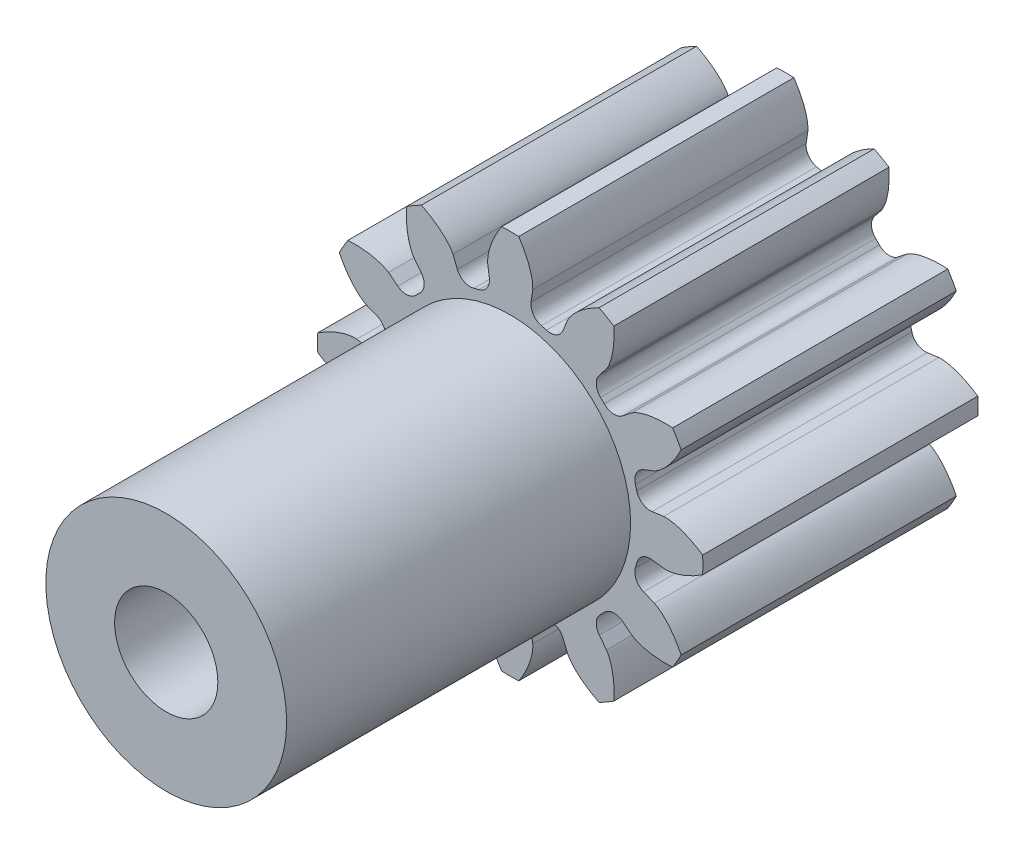
SolidWorks part; units mm, degrees
material "Brass"
ref_plane "Front Plane" through (0, 0, 0) normal (0, 0, 1) x (1, 0, 0)
ref_plane "Top Plane" through (0, 0, 0) normal (0, 1, 0) x (1, 0, 0)
ref_plane "Right Plane" through (0, 0, 0) normal (1, 0, 0) x (0, 0, -1)
ref_plane "Plane1" through (0, 0, 0) normal (0, 0, -1) x (-1, 0, 0)
sketch "Sketch1" plane through (0, 0, 0) normal (0, 0, -1) x (-1, 0, 0)
  line L0 (-2.3524, -2.9706) -> (-2.7989, -3.5371)
  line L1 (-1.6638, -4.1924) -> (-1.3964, -3.5225)
  line L2 (-0.5519, -3.7488) -> (-0.6553, -4.4627)
  line L3 (0.6553, -4.4627) -> (0.5519, -3.7488)
  line L4 (1.3964, -3.5225) -> (1.6638, -4.1924)
  line L5 (2.7989, -3.5371) -> (2.3524, -2.9706)
  line L6 (2.9706, -2.3524) -> (3.5371, -2.7989)
  line L7 (4.1924, -1.6638) -> (3.5225, -1.3964)
  line L8 (3.7488, -0.5519) -> (4.4627, -0.6553)
  line L9 (4.4627, 0.6553) -> (3.7488, 0.5519)
  line L10 (3.5225, 1.3964) -> (4.1924, 1.6638)
  line L11 (3.5371, 2.7989) -> (2.9706, 2.3524)
  line L12 (2.3524, 2.9706) -> (2.7989, 3.5371)
  line L13 (1.6638, 4.1924) -> (1.3964, 3.5225)
  line L14 (0.5519, 3.7488) -> (0.6553, 4.4627)
  line L15 (-0.6553, 4.4627) -> (-0.5519, 3.7488)
  line L16 (-1.3964, 3.5225) -> (-1.6638, 4.1924)
  line L17 (-2.7989, 3.5371) -> (-2.3524, 2.9706)
  line L18 (-2.9706, 2.3524) -> (-3.5371, 2.7989)
  line L19 (-4.1924, 1.6638) -> (-3.5225, 1.3964)
  line L20 (-3.7488, 0.5519) -> (-4.4627, 0.6553)
  line L21 (-4.4627, -0.6553) -> (-3.7488, -0.5519)
  line L22 (-3.5225, -1.3964) -> (-4.1924, -1.6638)
  line L23 (-3.5371, -2.7989) -> (-2.9706, -2.3524)
  arc A0 (-2.9706, -2.3524) -> (-2.3524, -2.9706) centre (0, 0) ccw
  arc A1 (-3.0123, -4.7208) -> (-2.5822, -4.9691) centre (0, 0) ccw
  arc A2 (-1.3964, -3.5225) -> (-0.5519, -3.7488) centre (0, 0) ccw
  arc A3 (-0.2483, -5.5945) -> (0.2483, -5.5945) centre (0, 0) ccw
  arc A4 (0.5519, -3.7488) -> (1.3964, -3.5225) centre (0, 0) ccw
  arc A5 (2.5822, -4.9691) -> (3.0123, -4.7208) centre (0, 0) ccw
  arc A6 (2.3524, -2.9706) -> (2.9706, -2.3524) centre (0, 0) ccw
  arc A7 (4.7208, -3.0123) -> (4.9691, -2.5822) centre (0, 0) ccw
  arc A8 (3.5225, -1.3964) -> (3.7488, -0.5519) centre (0, 0) ccw
  arc A9 (5.5945, -0.2483) -> (5.5945, 0.2483) centre (0, 0) ccw
  arc A10 (3.7488, 0.5519) -> (3.5225, 1.3964) centre (0, 0) ccw
  arc A11 (4.9691, 2.5822) -> (4.7208, 3.0123) centre (0, 0) ccw
  arc A12 (2.9706, 2.3524) -> (2.3524, 2.9706) centre (0, 0) ccw
  arc A13 (3.0123, 4.7208) -> (2.5822, 4.9691) centre (0, 0) ccw
  arc A14 (1.3964, 3.5225) -> (0.5519, 3.7488) centre (0, 0) ccw
  arc A15 (0.2483, 5.5945) -> (-0.2483, 5.5945) centre (0, 0) ccw
  arc A16 (-0.5519, 3.7488) -> (-1.3964, 3.5225) centre (0, 0) ccw
  arc A17 (-2.5822, 4.9691) -> (-3.0123, 4.7208) centre (0, 0) ccw
  arc A18 (-2.3524, 2.9706) -> (-2.9706, 2.3524) centre (0, 0) ccw
  arc A19 (-4.7208, 3.0123) -> (-4.9691, 2.5822) centre (0, 0) ccw
  arc A20 (-3.5225, 1.3964) -> (-3.7488, 0.5519) centre (0, 0) ccw
  arc A21 (-5.5945, 0.2483) -> (-5.5945, -0.2483) centre (0, 0) ccw
  arc A22 (-3.7488, -0.5519) -> (-3.5225, -1.3964) centre (0, 0) ccw
  arc A23 (-4.9691, -2.5822) -> (-4.7208, -3.0123) centre (0, 0) ccw
  ellipse E0 centre (-2.4375, -4.6593) end of major axis (-2.5173, -3.3364) minor radius 0.5776 (-2.7989, -3.5371) -> (-3.0123, -4.7208) ccw
  ellipse E1 centre (-2.8163, -4.4405) end of major axis (-4.0018, -5.0328) minor radius 0.5776 (-2.5822, -4.9691) -> (-1.6638, -4.1924) ccw
  ellipse E2 centre (0.2187, -5.2538) end of major axis (-0.5118, -4.1481) minor radius 0.5776 (-0.6553, -4.4627) -> (-0.2483, -5.5945) ccw
  ellipse E3 centre (-0.2187, -5.2538) end of major axis (-0.9493, -6.3595) minor radius 0.5776 (0.2483, -5.5945) -> (0.6553, -4.4627) ccw
  ellipse E4 centre (2.8163, -4.4405) end of major axis (4.0018, -5.0328) minor radius 0.5776 (1.6638, -4.1924) -> (2.5822, -4.9691) ccw
  ellipse E5 centre (2.4375, -4.6593) end of major axis (2.3576, -5.9821) minor radius 0.5776 (3.0123, -4.7208) -> (2.7989, -3.5371) ccw
  ellipse E6 centre (4.6593, -2.4375) end of major axis (3.3364, -2.5173) minor radius 0.5776 (3.5371, -2.7989) -> (4.7208, -3.0123) ccw
  ellipse E7 centre (4.4405, -2.8163) end of major axis (5.0328, -4.0018) minor radius 0.5776 (4.9691, -2.5822) -> (4.1924, -1.6638) ccw
  ellipse E8 centre (5.2538, 0.2187) end of major axis (4.1481, -0.5118) minor radius 0.5776 (4.4627, -0.6553) -> (5.5945, -0.2483) ccw
  ellipse E9 centre (5.2538, -0.2187) end of major axis (4.1481, 0.5118) minor radius 0.5776 (5.5945, 0.2483) -> (4.4627, 0.6553) ccw
  ellipse E10 centre (4.4405, 2.8163) end of major axis (5.0328, 4.0018) minor radius 0.5776 (4.1924, 1.6638) -> (4.9691, 2.5822) ccw
  ellipse E11 centre (4.6593, 2.4375) end of major axis (5.9821, 2.3576) minor radius 0.5776 (4.7208, 3.0123) -> (3.5371, 2.7989) ccw
  ellipse E12 centre (2.4375, 4.6593) end of major axis (2.3576, 5.9821) minor radius 0.5776 (2.7989, 3.5371) -> (3.0123, 4.7208) ccw
  ellipse E13 centre (2.8163, 4.4405) end of major axis (1.6308, 3.8483) minor radius 0.5776 (2.5822, 4.9691) -> (1.6638, 4.1924) ccw
  ellipse E14 centre (-0.2187, 5.2538) end of major axis (-0.9493, 6.3595) minor radius 0.5776 (0.6553, 4.4627) -> (0.2483, 5.5945) ccw
  ellipse E15 centre (0.2187, 5.2538) end of major axis (-0.5118, 4.1481) minor radius 0.5776 (-0.2483, 5.5945) -> (-0.6553, 4.4627) ccw
  ellipse E16 centre (-2.8163, 4.4405) end of major axis (-4.0018, 5.0328) minor radius 0.5776 (-1.6638, 4.1924) -> (-2.5822, 4.9691) ccw
  ellipse E17 centre (-2.4375, 4.6593) end of major axis (-2.5173, 3.3364) minor radius 0.5776 (-3.0123, 4.7208) -> (-2.7989, 3.5371) ccw
  ellipse E18 centre (-4.6593, 2.4375) end of major axis (-5.9821, 2.3576) minor radius 0.5776 (-3.5371, 2.7989) -> (-4.7208, 3.0123) ccw
  ellipse E19 centre (-4.4405, 2.8163) end of major axis (-3.8483, 1.6308) minor radius 0.5776 (-4.9691, 2.5822) -> (-4.1924, 1.6638) ccw
  ellipse E20 centre (-5.2538, -0.2187) end of major axis (-6.3595, -0.9493) minor radius 0.5776 (-4.4627, 0.6553) -> (-5.5945, 0.2483) ccw
  ellipse E21 centre (-5.2538, 0.2187) end of major axis (-6.3595, 0.9493) minor radius 0.5776 (-5.5945, -0.2483) -> (-4.4627, -0.6553) ccw
  ellipse E22 centre (-4.4405, -2.8163) end of major axis (-3.8483, -1.6308) minor radius 0.5776 (-4.1924, -1.6638) -> (-4.9691, -2.5822) ccw
  ellipse E23 centre (-4.6593, -2.4375) end of major axis (-5.9821, -2.3576) minor radius 0.5776 (-4.7208, -3.0123) -> (-3.5371, -2.7989) ccw
  point P4 (-2.4375, -4.6593)
  point P5 (-3.014, -4.6941)
  point P6 (-2.5173, -3.3364)
  point P7 (-2.7989, -3.5371)
  point P8 (-3.0123, -4.7208)
  point P9 (-2.9867, -4.0852)
  point P10 (-1.8883, -5.2334)
  point P18 (-2.8163, -4.4405)
  point P19 (-4.0018, -5.0328)
  point P20 (-2.5582, -4.9572)
  point P21 (-2.5822, -4.9691)
  point P22 (-1.6638, -4.1924)
  point P23 (-2.0445, -4.6291)
  point P24 (-3.5881, -4.252)
  point P34 (0.2187, -5.2538)
  point P35 (-0.2632, -5.5722)
  point P36 (-0.5118, -4.1481)
  point P37 (-0.6553, -4.4627)
  point P38 (-0.2483, -5.5945)
  point P39 (-0.5439, -5.0312)
  point P40 (0.9814, -5.4764)
  point P48 (-0.2187, -5.2538)
  point P49 (-0.7006, -4.9354)
  point P50 (-0.9493, -6.3595)
  point P51 (0.2483, -5.5945)
  point P52 (0.6553, -4.4627)
  point P53 (0.5439, -5.0312)
  point P54 (-0.9814, -5.4764)
  point P64 (2.8163, -4.4405)
  point P65 (1.6308, -3.8483)
  point P66 (3.0744, -3.9238)
  point P67 (1.6638, -4.1924)
  point P68 (2.5822, -4.9691)
  point P69 (2.0445, -4.6291)
  point P70 (3.5881, -4.252)
  point P78 (2.4375, -4.6593)
  point P79 (1.8609, -4.6245)
  point P80 (2.3576, -5.9821)
  point P81 (3.0123, -4.7208)
  point P82 (2.7989, -3.5371)
  point P83 (2.9867, -4.0852)
  point P84 (1.8883, -5.2334)
  point P94 (4.6593, -2.4375)
  point P95 (3.3364, -2.5173)
  point P96 (4.6245, -1.8609)
  point P97 (3.5371, -2.7989)
  point P98 (4.7208, -3.0123)
  point P99 (4.0852, -2.9867)
  point P100 (5.2334, -1.8883)
  point P108 (4.4405, -2.8163)
  point P109 (3.9238, -3.0744)
  point P110 (5.0328, -4.0018)
  point P111 (4.9691, -2.5822)
  point P112 (4.1924, -1.6638)
  point P113 (4.6291, -2.0445)
  point P114 (4.252, -3.5881)
  point P124 (5.2538, 0.2187)
  point P125 (4.1481, -0.5118)
  point P126 (4.9354, 0.7006)
  point P127 (4.4627, -0.6553)
  point P128 (5.5945, -0.2483)
  point P129 (5.0312, -0.5439)
  point P130 (5.4764, 0.9814)
  point P138 (5.2538, -0.2187)
  point P139 (4.1481, 0.5118)
  point P140 (4.9354, -0.7006)
  point P141 (5.5945, 0.2483)
  point P142 (4.4627, 0.6553)
  point P143 (5.0312, 0.5439)
  point P144 (5.4764, -0.9814)
  point P154 (4.4405, 2.8163)
  point P155 (3.9238, 3.0744)
  point P156 (5.0328, 4.0018)
  point P157 (4.1924, 1.6638)
  point P158 (4.9691, 2.5822)
  point P159 (4.6291, 2.0445)
  point P160 (4.252, 3.5881)
  point P168 (4.6593, 2.4375)
  point P169 (3.3364, 2.5173)
  point P170 (4.6245, 1.8609)
  point P171 (4.7208, 3.0123)
  point P172 (3.5371, 2.7989)
  point P173 (4.0852, 2.9867)
  point P174 (5.2334, 1.8883)
  point P184 (2.4375, 4.6593)
  point P185 (1.8609, 4.6245)
  point P186 (2.3576, 5.9821)
  point P187 (2.7989, 3.5371)
  point P188 (3.0123, 4.7208)
  point P189 (2.9867, 4.0852)
  point P190 (1.8883, 5.2334)
  point P198 (2.8163, 4.4405)
  point P199 (1.6308, 3.8483)
  point P200 (3.0744, 3.9238)
  point P201 (2.5822, 4.9691)
  point P202 (1.6638, 4.1924)
  point P203 (2.0445, 4.6291)
  point P204 (3.5881, 4.252)
  point P214 (-0.2187, 5.2538)
  point P215 (-0.7006, 4.9354)
  point P216 (-0.9493, 6.3595)
  point P217 (0.6553, 4.4627)
  point P218 (0.2483, 5.5945)
  point P219 (0.5439, 5.0312)
  point P220 (-0.9814, 5.4764)
  point P228 (0.2187, 5.2538)
  point P229 (-0.2632, 5.5722)
  point P230 (-0.5118, 4.1481)
  point P231 (-0.2483, 5.5945)
  point P232 (-0.6553, 4.4627)
  point P233 (-0.5439, 5.0312)
  point P234 (0.9814, 5.4764)
  point P244 (-2.8163, 4.4405)
  point P245 (-4.0018, 5.0328)
  point P246 (-2.5582, 4.9572)
  point P247 (-1.6638, 4.1924)
  point P248 (-2.5822, 4.9691)
  point P249 (-2.0445, 4.6291)
  point P250 (-3.5881, 4.252)
  point P258 (-2.4375, 4.6593)
  point P259 (-3.014, 4.6941)
  point P260 (-2.5173, 3.3364)
  point P261 (-3.0123, 4.7208)
  point P262 (-2.7989, 3.5371)
  point P263 (-2.9867, 4.0852)
  point P264 (-1.8883, 5.2334)
  point P274 (-4.6593, 2.4375)
  point P275 (-5.9821, 2.3576)
  point P276 (-4.6941, 3.014)
  point P277 (-3.5371, 2.7989)
  point P278 (-4.7208, 3.0123)
  point P279 (-4.0852, 2.9867)
  point P280 (-5.2334, 1.8883)
  point P288 (-4.4405, 2.8163)
  point P289 (-4.9572, 2.5582)
  point P290 (-3.8483, 1.6308)
  point P291 (-4.9691, 2.5822)
  point P292 (-4.1924, 1.6638)
  point P293 (-4.6291, 2.0445)
  point P294 (-4.252, 3.5881)
  point P304 (-5.2538, -0.2187)
  point P305 (-6.3595, -0.9493)
  point P306 (-5.5722, 0.2632)
  point P307 (-4.4627, 0.6553)
  point P308 (-5.5945, 0.2483)
  point P309 (-5.0312, 0.5439)
  point P310 (-5.4764, -0.9814)
  point P318 (-5.2538, 0.2187)
  point P319 (-6.3595, 0.9493)
  point P320 (-5.5722, -0.2632)
  point P321 (-5.5945, -0.2483)
  point P322 (-4.4627, -0.6553)
  point P323 (-5.0312, -0.5439)
  point P324 (-5.4764, 0.9814)
  point P334 (-4.4405, -2.8163)
  point P335 (-4.9572, -2.5582)
  point P336 (-3.8483, -1.6308)
  point P337 (-4.1924, -1.6638)
  point P338 (-4.9691, -2.5822)
  point P339 (-4.6291, -2.0445)
  point P340 (-4.252, -3.5881)
  point P348 (-4.6593, -2.4375)
  point P349 (-5.9821, -2.3576)
  point P350 (-4.6941, -3.014)
  point P351 (-4.7208, -3.0123)
  point P352 (-3.5371, -2.7989)
  point P353 (-4.0852, -2.9867)
  point P354 (-5.2334, -1.8883)
extrude "Boss-Extrude1" add sketch "Sketch1" against normal blind 8
sketch "Sketch2" plane through (0, 0, 0) normal (0, 1, 0) x (1, 0, 0)
  line L0 (3.5, -8) -> (0, -8)
  line L1 (0, -8) -> (0, -18)
  line L2 (0, -18) -> (3.5, -18)
  line L3 (3.5, -18) -> (3.5, -8)
  line L4 (0, -8) -> (0, -18) construction
revolve "Revolve1" add sketch "Sketch2" angle 360 about L4
hole_wizard "Ø3.0 (3) Diameter Hole1" positions "Sketch4" profile "Sketch3" hole size "Ø3.0" standard "ANSI Metric"
sketch "Sketch4" plane through (0, 0, 18) normal (0, 0, 1) x (1, 0, 0)
  point P0 (0, 0)
sketch "Sketch3" plane through (0, 0, 18) normal (1, 0, 0) x (0, -1, 0)
  line L0 (0, 0) -> (0, 18)
  line L1 (0, 18) -> (1.5, 18)
  line L2 (1.5, 18) -> (1.5, 0)
  line L5 (1.5, 0) -> (0, 0)
  line L11 (0, -6.35) -> (0, 107.95) construction
  dimension "Thru Hole Dia." = 3
  dimension "Thru Hole Depth" = 18
ref_plane "Plane2" through (0, 0.8069, 0) normal (0, -1, 0) x (-1, 0, 0)
fillet "Fillet1" radius 0.4 24 edges at (-1.3964, 3.5225, 4) (3.7488, -0.5519, 4) (2.3524, 2.9706, 4) (2.9706, -2.3524, 4) (-2.9706, 2.3524, 4) (2.3524, -2.9706, 4) (0.5519, 3.7488, 4) (1.3964, -3.5225, 4) (3.5225, 1.3964, 4) (0.5519, -3.7488, 4) (-3.5225, 1.3964, 4) (-0.5519, -3.7488, 4) (-2.3524, 2.9706, 4) (-1.3964, -3.5225, 4) (-0.5519, 3.7488, 4) (-2.3524, -2.9706, 4) (1.3964, 3.5225, 4) (-2.9706, -2.3524, 4) (2.9706, 2.3524, 4) (-3.5225, -1.3964, 4) (3.7488, 0.5519, 4) (-3.7488, -0.5519, 4) (3.5225, -1.3964, 4) (-3.7488, 0.5519, 4)
sketch "Sketch5" plane through (0, 0, 0) normal (0, 1, 0) x (1, 0, 0)
  line L0 (-3.5, -18) -> (3.5, -18) construction
  circle A0 centre (0, -14) radius 1.25
  dimension "D2" = 2.5
  dimension "D1" = 4
extrude "Cut-Extrude1" cut sketch "Sketch5" against normal blind 10
